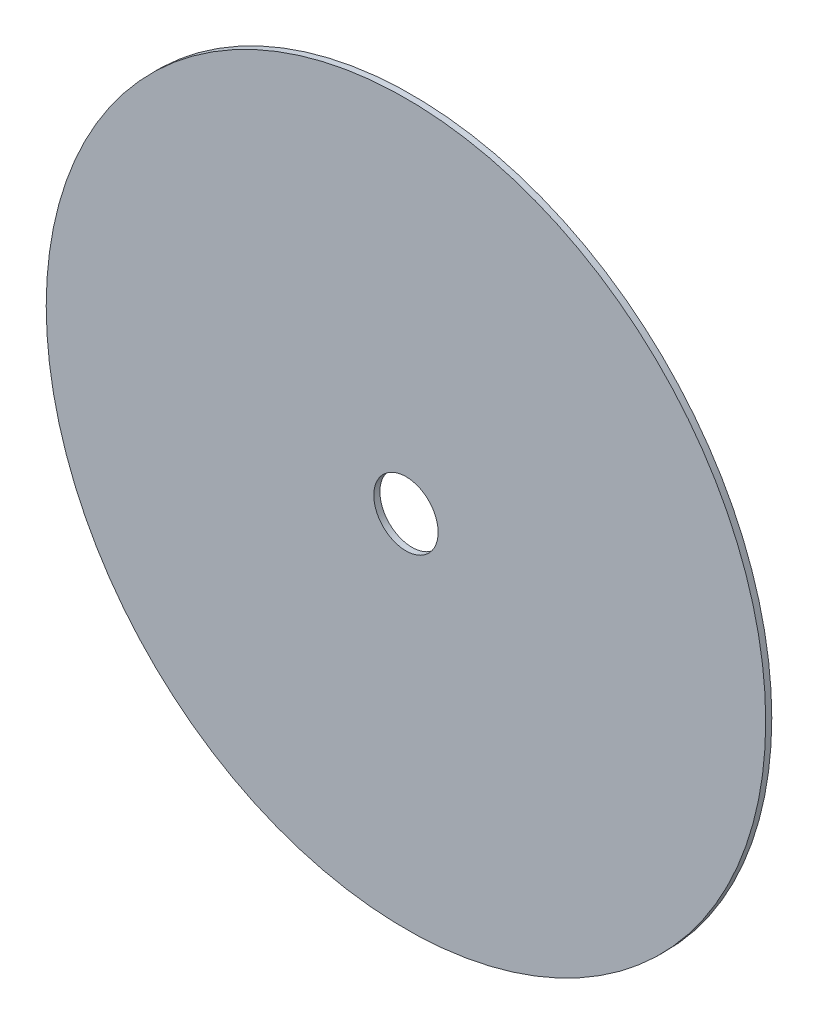
SolidWorks part; units mm, degrees
ref_plane "Front Plane" through (0, 0, 0) normal (0, 0, 1) x (1, 0, 0)
ref_plane "Top Plane" through (0, 0, 0) normal (0, 1, 0) x (1, 0, 0)
ref_plane "Right Plane" through (0, 0, 0) normal (1, 0, 0) x (0, 0, -1)
sketch "Sketch1" plane through (0, 0, 0) normal (0, 0, 1) x (1, 0, 0)
  circle A0 centre (0, 0) radius 177.8
  circle A1 centre (0, 0) radius 15.9
  dimension "D1" = 355.6
extrude "Boss-Extrude1" add sketch "Sketch1" along normal blind 3
